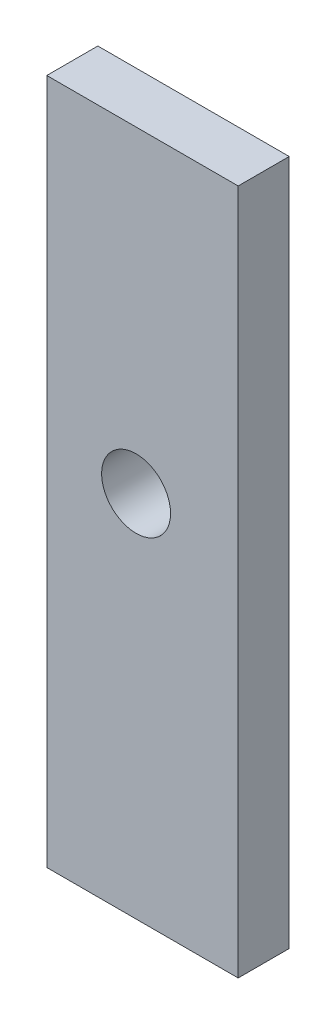
SolidWorks part; units mm, degrees
ref_plane "Front Plane" through (0, 0, 0) normal (0, 0, 1) x (1, 0, 0)
ref_plane "Top Plane" through (0, 0, 0) normal (0, 1, 0) x (1, 0, 0)
ref_plane "Right Plane" through (0, 0, 0) normal (1, 0, 0) x (0, 0, -1)
sketch "Sketch1" plane through (0, 0, 0) normal (0, 0, 1) x (1, 0, 0)
  line L0 (-3.5, 12.44) -> (4, 12.44)
  line L1 (-3.5, -14.441) -> (4, -14.441)
  line L2 (4, -14.441) -> (4, 12.44)
  line L3 (-3.5, 12.44) -> (-3.5, -14.441)
  circle A0 centre (0, 0) radius 1.35
  dimension "D1" = 2.7
  dimension "D4" = 12.44
  dimension "D2" = 4
  dimension "D3" = 3.5
  dimension "D5" = 14.441
extrude "Boss-Extrude1" add sketch "Sketch1" along normal blind 2
equation "\"D5@Sketch1\" = \"D76@Sketch1@palmUp-1.Part\" - 6.72 - 0.41'Support Pully Thumb Palm Up"
equation "\"D1@Sketch1\"= 3 - \"tol1@parametersSketch@prostheticParameters.SLDPRT\""
